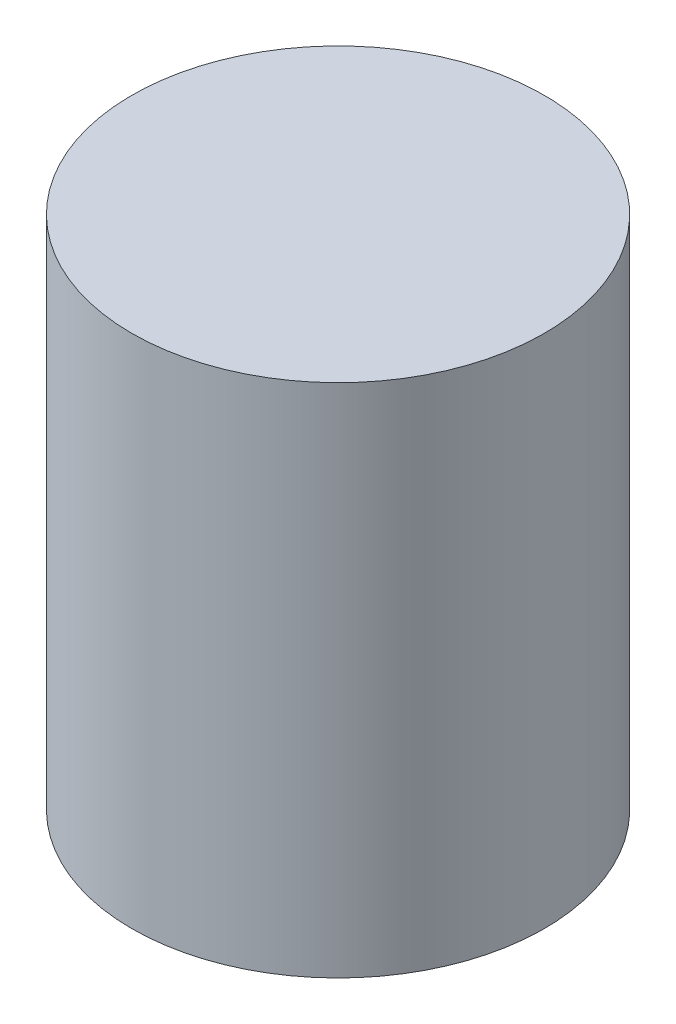
SolidWorks part; units mm, degrees
material "3.1355 (EN-AW 2024)"
ref_plane "Front" through (0, 0, 0) normal (0, 0, 1) x (1, 0, 0)
ref_plane "Top" through (0, 0, 0) normal (0, 1, 0) x (1, 0, 0)
ref_plane "Right" through (0, 0, 0) normal (1, 0, 0) x (0, 0, -1)
sketch "Эскиз1" plane through (0, 0, 0) normal (0, 1, 0) x (1, 0, 0)
  circle A0 centre (0, 0) radius 10
  dimension "D1" = 20
extrude "Бобышка-Вытянуть1" add sketch "Эскиз1" along normal blind 25
